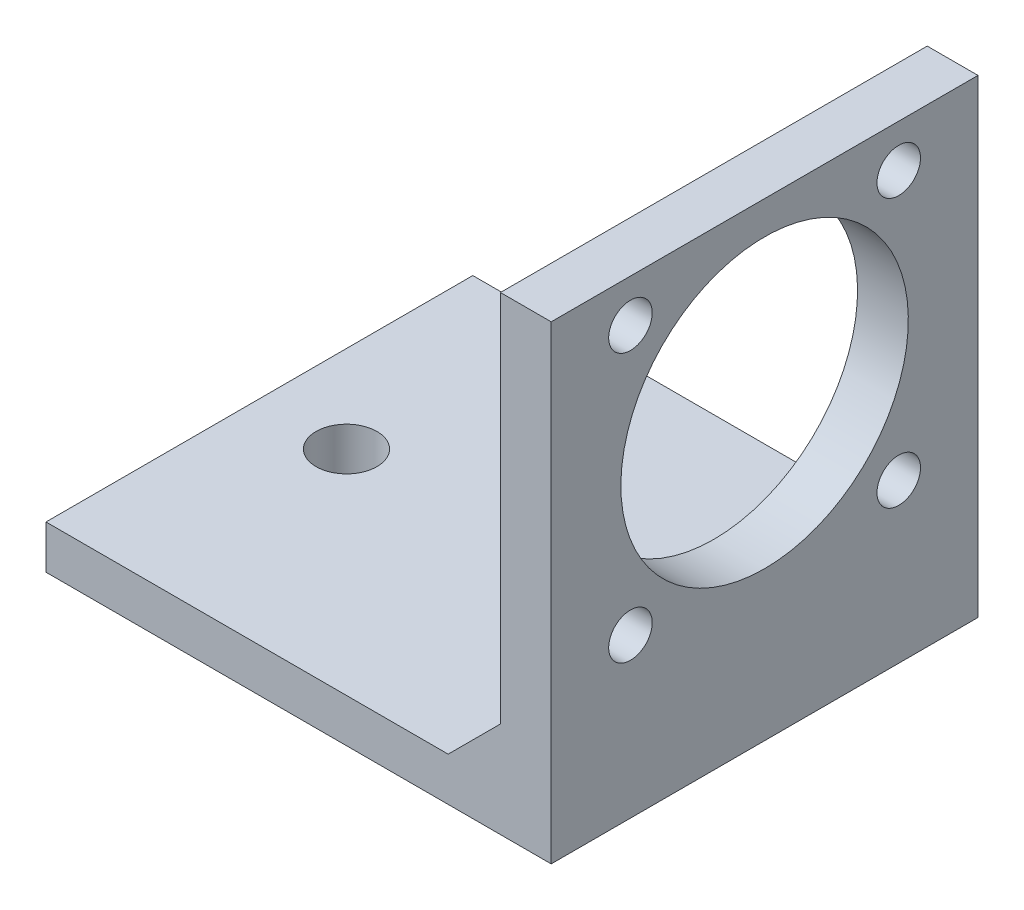
SolidWorks part; units mm, degrees
ref_plane "Front Plane" through (0, 0, 0) normal (0, 0, 1) x (1, 0, 0)
ref_plane "Top Plane" through (0, 0, 0) normal (0, 1, 0) x (1, 0, 0)
ref_plane "Right Plane" through (0, 0, 0) normal (1, 0, 0) x (0, 0, -1)
sketch "Sketch1" plane through (0, 0, 0) normal (0, 0, 1) x (1, 0, 0)
  line L1 (0, 0) -> (29, 0)
  line L2 (0, 0) -> (0, 2.5)
  line L3 (0, 2.5) -> (29, 2.5)
  line L4 (29, 0) -> (29, 2.5)
  line L5 (29, 2.5) -> (26.0857, 2.5)
  line L6 (29, 2.5) -> (29, 27.5)
  line L7 (29, 27.5) -> (26.0857, 27.5)
  line L8 (26.0857, 2.5) -> (26.0857, 27.5)
  dimension "D1" = 29
  dimension "D2" = 2.5
  dimension "D3" = 25
extrude "Boss-Extrude1" add sketch "Sketch1" along normal blind 24.5 contours L8 L3 L6 L7 | L1 L4 L3 L2
sketch "Sketch2" plane through (29, 0, 0) normal (1, 0, 0) x (0, 0, -1)
  line L1 (-24.5, 0) -> (-24.5, 27.5) construction
  line L3 (0, 0) -> (0, 27.5) construction
  line L4 (-24.5, 27.5) -> (0, 27.5) construction
  circle A0 centre (-19.95, 24.5) radius 1.25
  circle A1 centre (-4.55, 24.5) radius 1.25
  circle A2 centre (-4.55, 9.1) radius 1.25
  circle A3 centre (-19.95, 9.1) radius 1.25
  dimension "D1" = 2.5
  dimension "D4" = 15.4
  dimension "D6" = 4.55
  dimension "D8" = 3
  dimension "D2" = 15.4
  dimension "D3" = 15.4
  dimension "D5" = 15.4
  dimension "D7" = 4.55
extrude "Cut-Extrude1" cut sketch "Sketch2" against normal through all
sketch "Sketch3" plane through (0, 2.5, 0) normal (0, 1, 0) x (1, 0, 0)
  line L0 (0, -12.25) -> (20, -12.25)
  line L1 (0, -24.5) -> (0, 0) construction
  circle A0 centre (5, -12.25) radius 1.75
  circle A1 centre (20, -12.25) radius 1.75
  dimension "D1" = 3.5
  dimension "D2" = 15
  dimension "D3" = 5
extrude "Cut-Extrude2" cut sketch "Sketch3" against normal through all both and the other way through all
sketch "Sketch4" plane through (26.0857, 0, 0) normal (-1, 0, 0) x (0, 0, 1)
  circle A0 centre (12.25, 16.8) radius 8.25
  circle A1 centre (19.95, 24.5) radius 1.25 construction
  dimension "D1" = 16.5
  dimension "D2" = 7.7
  dimension "D3" = 7.7
extrude "Cut-Extrude3" cut sketch "Sketch4" against normal through all both and the other way through all
sketch "Sketch5" plane through (0, 0, 24.5) normal (0, 0, 1) x (1, 0, 0)
  line L0 (29, 0) -> (29, 27.5) construction
  line L1 (26.0857, 27.5) -> (29, 27.5)
  line L2 (26.0857, 27.5) -> (26.0857, 26.95)
  line L3 (26.0857, 26.95) -> (29, 26.95)
  line L4 (29, 27.5) -> (29, 26.95)
  dimension "D1" = 0.55
extrude "Cut-Extrude4" cut sketch "Sketch5" against normal through all both
chamfer "Chamfer1" distance 3 angle 45 1 edges at (26.0857, 2.5, 12.25)
